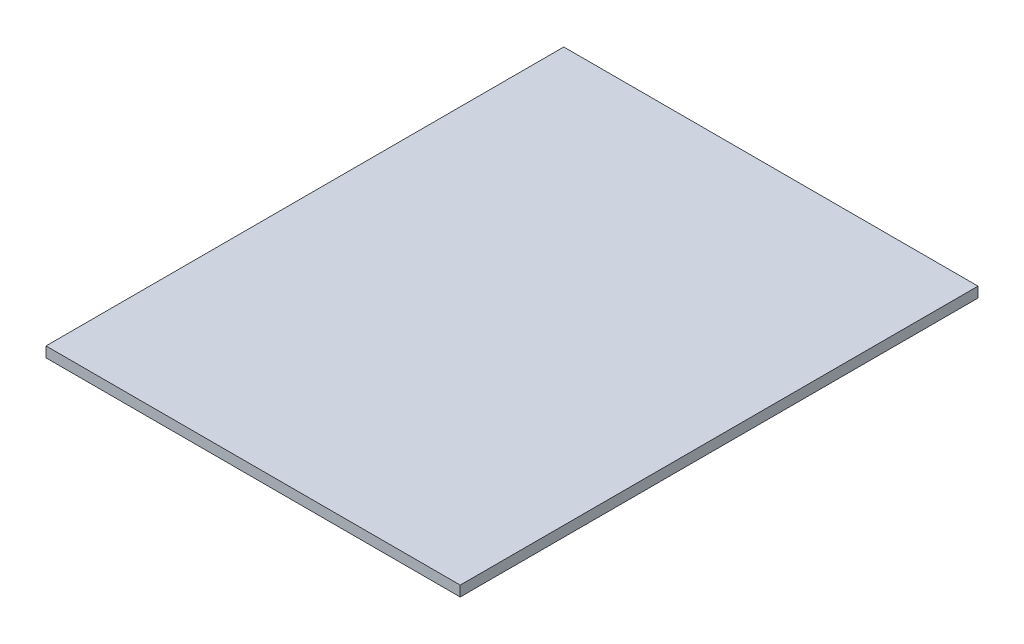
SolidWorks part; units mm, degrees
ref_plane "Front Plane" through (0, 0, 0) normal (0, 0, 1) x (1, 0, 0)
ref_plane "Top Plane" through (0, 0, 0) normal (0, 1, 0) x (1, 0, 0)
ref_plane "Right Plane" through (0, 0, 0) normal (1, 0, 0) x (0, 0, -1)
sketch "Sketch1" plane through (0, 0, 0) normal (0, 1, 0) x (1, 0, 0)
  line L0 (10387.4426, -3483.5479) -> (10417.4426, -3483.5479) construction
  line L1 (10302.4426, -3358.5479) -> (10502.4426, -3358.5479)
  line L2 (10302.4426, -3358.5479) -> (10302.4426, -3608.5479)
  line L3 (10302.4426, -3608.5479) -> (10502.4426, -3608.5479)
  line L4 (10502.4426, -3358.5479) -> (10502.4426, -3608.5479)
  line L5 (10302.4426, -3358.5479) -> (10502.4426, -3608.5479) construction
  line L6 (10302.4426, -3608.5479) -> (10502.4426, -3358.5479) construction
  point P4 (10402.4426, -3483.5479)
  dimension "D1" = 250
  dimension "D2" = 200
extrude "Boss-Extrude1" add sketch "Sketch1" along normal blind 5
